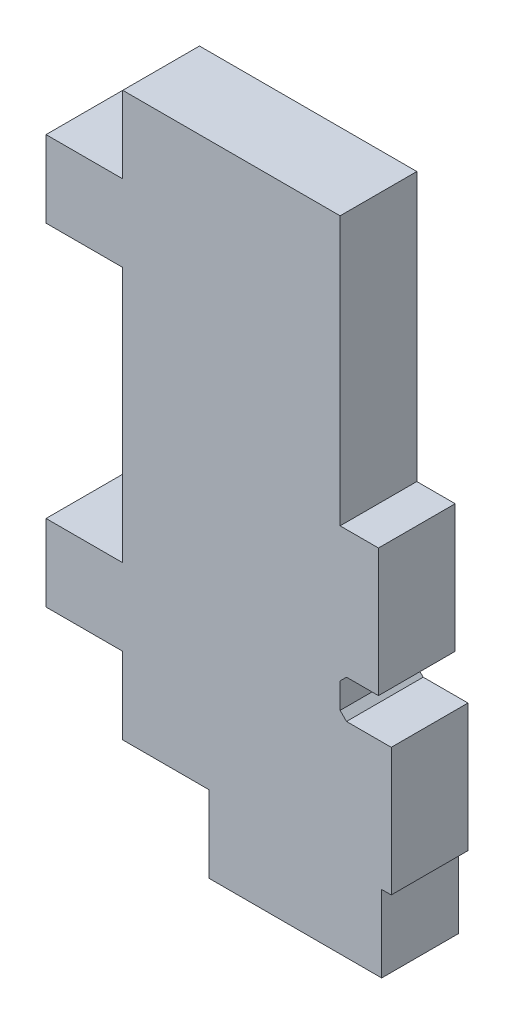
SolidWorks part; units mm, degrees
ref_plane "Front Plane" through (0, 0, 0) normal (0, 0, 1) x (1, 0, 0)
ref_plane "Top Plane" through (0, 0, 0) normal (0, 1, 0) x (1, 0, 0)
ref_plane "Right Plane" through (0, 0, 0) normal (1, 0, 0) x (0, 0, -1)
sketch "Sketch1" plane through (0, 0, 0) normal (0, 0, 1) x (1, 0, 0)
  line L1 (-3.75, 11) -> (6.75, 11)
  line L2 (-3.75, 11) -> (-3.75, -11)
  line L3 (-3.75, -11) -> (6.75, -11)
  line L4 (6.75, 11) -> (6.75, -11)
  point P0 (0, 0)
  dimension "D1" = 10.5
  dimension "D2" = 22
extrude "Boss-Extrude1" add sketch "Sketch1" along normal blind 3
sketch "Sketch2" plane through (0, -11, 0) normal (0, -1, 0) x (1, 0, 0)
  line L0 (-3.75, 3) -> (6.75, 3) construction
  line L1 (-0.375, 3) -> (6.375, 3)
  line L2 (-0.375, 3) -> (-0.375, 0)
  line L3 (-0.375, 0) -> (6.375, 0)
  line L4 (6.375, 3) -> (6.375, 0)
  line L5 (-3.75, 0) -> (6.75, 0) construction
  line L6 (-3.75, 3) -> (-3.75, 0) construction
  dimension "D1" = 6.75
  dimension "D2" = 3.375
extrude "Boss-Extrude2" add sketch "Sketch2" along normal blind 3
sketch "Sketch3" plane through (-3.75, 0, 0) normal (-1, 0, 0) x (0, 0, 1)
  line L0 (0, 11) -> (0, -11) construction
  line L1 (0, -8) -> (3, -8)
  line L2 (0, -8) -> (0, -5)
  line L3 (0, -5) -> (3, -5)
  line L4 (3, -8) -> (3, -5)
  line L5 (3, 11) -> (3, -11) construction
  line L6 (3, 11) -> (0, 11) construction
  line L7 (0, 8) -> (3, 8)
  line L8 (0, 8) -> (0, 5)
  line L9 (0, 5) -> (3, 5)
  line L10 (3, 8) -> (3, 5)
  line L11 (3, -11) -> (0, -11) construction
  dimension "D1" = 3
  dimension "D2" = 3
  dimension "D3" = 3
  dimension "D4" = 3
extrude "Boss-Extrude3" add sketch "Sketch3" along normal blind 3
sketch "Sketch4" plane through (0, 0, 3) normal (0, 0, 1) x (1, 0, 0)
  line L0 (6.75, -11) -> (6.75, 11) construction
  line L1 (6.75, -4.5) -> (4.75, -4.5)
  line L2 (6.75, -4.5) -> (6.75, -6)
  line L3 (6.75, -6) -> (4.75, -6)
  line L4 (4.75, -4.5) -> (4.75, -6)
  line L5 (6.375, -11) -> (6.75, -11) construction
  dimension "D1" = 1.5
  dimension "D2" = 2
  dimension "D3" = 5
extrude "Cut-Extrude1" cut sketch "Sketch4" against normal blind 3
sketch "Sketch5" plane through (0, 0, 3) normal (0, 0, 1) x (1, 0, 0)
  line L0 (6.75, -4.5) -> (4.75, -4.5) construction
  line L1 (6.75, 11) -> (4.75, 11)
  line L2 (6.75, 11) -> (6.75, 0.5)
  line L3 (6.75, 0.5) -> (4.75, 0.5)
  line L4 (4.75, 11) -> (4.75, 0.5)
  dimension "D1" = 5
extrude "Cut-Extrude2" cut sketch "Sketch5" against normal blind 3
chamfer "Chamfer1" distance 0.25 angle 45 1 edges at (4.75, -4.5, 1.5)
chamfer "Chamfer2" distance 0.25 angle 45 1 edges at (4.75, -6, 1.5)
sketch "Sketch6" plane through (6.75, 0, 0) normal (1, 0, 0) x (0, 0, -1)
  line L1 (-3, 0.5) -> (0, 0.5)
  line L2 (-3, 0.5) -> (-3, -4.5)
  line L3 (-3, -4.5) -> (0, -4.5)
  line L4 (0, 0.5) -> (0, -4.5)
extrude "Cut-Extrude3" cut sketch "Sketch6" against normal blind 0.5
